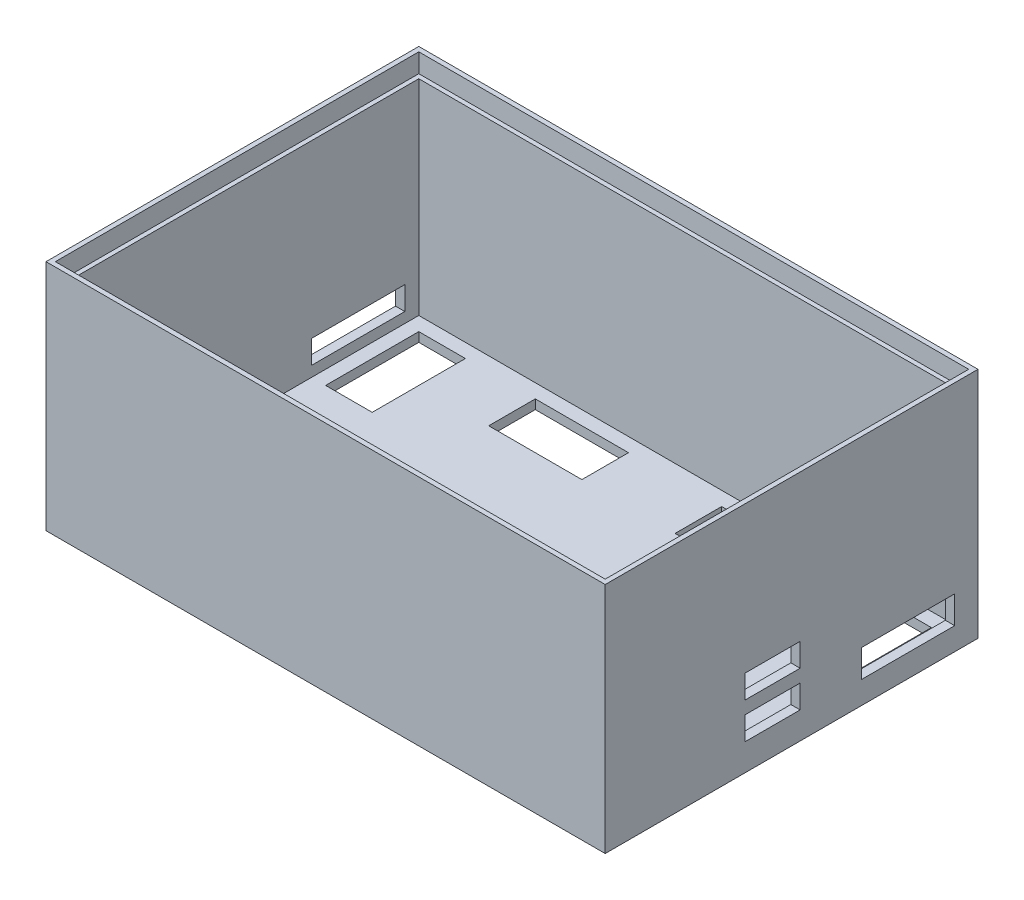
SolidWorks part; units mm, degrees
ref_plane "Front Plane" through (0, 0, 0) normal (0, 0, 1) x (1, 0, 0)
ref_plane "Top Plane" through (0, 0, 0) normal (0, 1, 0) x (1, 0, 0)
ref_plane "Right Plane" through (0, 0, 0) normal (1, 0, 0) x (0, 0, -1)
sketch "Sketch1" plane through (0, 0, 0) normal (0, 1, 0) x (1, 0, 0)
  line L1 (-60, 40) -> (60, 40)
  line L2 (-60, 40) -> (-60, -40)
  line L3 (-60, -40) -> (60, -40)
  line L4 (60, 40) -> (60, -40)
  line L5 (-60, 40) -> (60, -40) construction
  line L6 (-60, -40) -> (60, 40) construction
  point P0 (0, 0)
  dimension "D1" = 120
  dimension "D2" = 80
extrude "Boss-Extrude1" add sketch "Sketch1" along normal blind 50
shell "Shell1" thickness 2
sketch "Sketch3" plane through (0, 0, 0) normal (0, -1, 0) x (1, 0, 0)
  line L0 (-66.8213, 0) -> (0, 0) construction
  line L1 (0, 0) -> (0, 42.8035) construction
  line L2 (-60, -40) -> (-60, 40) construction
  line L3 (-18.8, 33.0135) -> (18.8, 33.0135)
  line L4 (-18.8, 33.0135) -> (-18.8, 14.0135)
  line L5 (-18.8, 14.0135) -> (18.8, 14.0135)
  line L6 (18.8, 33.0135) -> (18.8, 14.0135)
  line L7 (-18.8, 33.0135) -> (18.8, 14.0135) construction
  line L8 (-18.8, 14.0135) -> (18.8, 33.0135) construction
  line L9 (60, -40) -> (-60, -40) construction
  line L10 (-55, -15) -> (-45, -15)
  line L11 (-55, -15) -> (-55, -35)
  line L12 (-55, -35) -> (-45, -35)
  line L13 (-45, -15) -> (-45, -35)
  line L14 (30, -35) -> (10, -35)
  line L15 (-30, -25) -> (-10, -25)
  line L16 (-30, -25) -> (-30, -35)
  line L17 (-30, -35) -> (-10, -35)
  line L18 (-10, -25) -> (-10, -35)
  line L19 (10, -25) -> (10, -35)
  line L20 (30, -25) -> (10, -25)
  line L21 (30, -25) -> (30, -35)
  line L22 (55, -35) -> (45, -35)
  line L23 (45, -15) -> (45, -35)
  line L24 (55, -15) -> (45, -15)
  line L25 (55, -15) -> (55, -35)
  circle A2 centre (-50, 31.648) radius 2.5
  circle A3 centre (-50, 23.108) radius 2.5
  point P3 (0, 23.5135)
  dimension "D3" = 5
  dimension "D1" = 19
  dimension "D2" = 37.6
  dimension "D4" = 10
  dimension "D5" = 10
  dimension "D6" = 10
  dimension "D7" = 20
  dimension "D8" = 5
  dimension "D9" = 5
  dimension "D10" = 20
  dimension "D11" = 10
  dimension "D12" = 5
  dimension "D13" = 30
extrude "Cut-Extrude1" cut sketch "Sketch3" against normal blind 2
sketch "Sketch4" plane through (-60, 0, 0) normal (-1, 0, 0) x (0, 0, 1)
  line L0 (-40, 50) -> (-40, 0) construction
  line L1 (-40, 0) -> (40, 0) construction
  line L11 (-35, 9.2403) -> (-15, 9.2403)
  line L12 (-35, 9.2403) -> (-35, 4.2403)
  line L13 (-35, 4.2403) -> (-15, 4.2403)
  line L14 (-15, 9.2403) -> (-15, 4.2403)
  circle A0 centre (5, 10) radius 3.5
  dimension "D1" = 7
  dimension "D2" = 45
  dimension "D3" = 10
  dimension "D4" = 5
  dimension "D5" = 20
  dimension "D6" = 5
extrude "Cut-Extrude2" cut sketch "Sketch4" against normal blind 2
sketch "Sketch5" plane through (0, 50, 0) normal (0, 1, 0) x (1, 0, 0)
  line L8 (59, -39) -> (59, 39)
  line L9 (59, 39) -> (-59, 39)
  line L10 (-59, 39) -> (-59, -39)
  line L11 (-59, -39) -> (59, -39)
  line L12 (59, -39) -> (59, 39)
  line L13 (59, 39) -> (-59, 39)
  line L14 (-59, 39) -> (-59, -39)
  line L15 (-59, -39) -> (59, -39)
  dimension "D1" = 1
extrude "Cut-Extrude3" cut sketch "Sketch5" against normal blind 4 draft 1
sketch "Sketch6" plane through (60, 0, 0) normal (1, 0, 0) x (0, 0, -1)
  line L0 (40, 50) -> (40, 0) construction
  line L1 (-10.0056, 10.7803) -> (1.836, 10.7803)
  line L2 (-10.0056, 10.7803) -> (-10.0056, 5.7803)
  line L3 (-10.0056, 5.7803) -> (1.836, 5.7803)
  line L4 (1.836, 10.7803) -> (1.836, 5.7803)
  line L5 (-10.0056, 18.5269) -> (1.836, 18.5269)
  line L6 (-10.0056, 18.5269) -> (-10.0056, 13.5269)
  line L7 (-10.0056, 13.5269) -> (1.836, 13.5269)
  line L8 (1.836, 18.5269) -> (1.836, 13.5269)
  line L9 (15, 10.7803) -> (35, 10.7803)
  line L10 (15, 10.7803) -> (15, 4.8526)
  line L11 (15, 4.8526) -> (35, 4.8526)
  line L12 (35, 10.7803) -> (35, 4.8526)
  dimension "D1" = 5
  dimension "D2" = 5
  dimension "5" = 5
  dimension "D3" = 20
extrude "Cut-Extrude4" cut sketch "Sketch6" against normal blind 4
